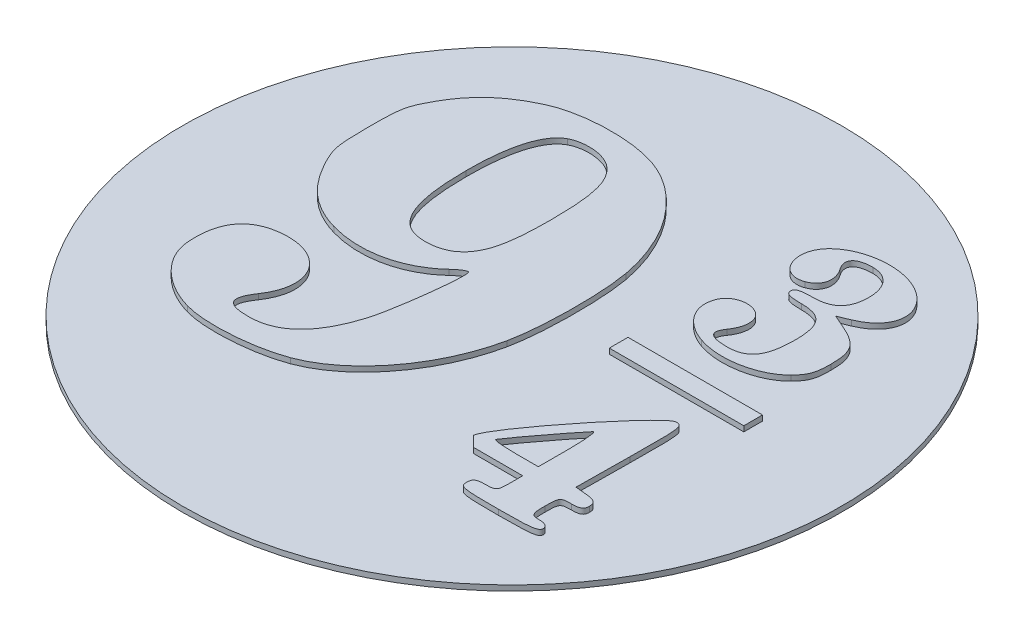
SolidWorks part; units mm, degrees
ref_plane "前视基准面" through (0, 0, 0) normal (0, 0, 1) x (1, 0, 0)
ref_plane "上视基准面" through (0, 0, 0) normal (0, 1, 0) x (1, 0, 0)
ref_plane "右视基准面" through (0, 0, 0) normal (1, 0, 0) x (0, 0, -1)
other "Configuration Table"
sketch "草图1" plane through (0, 0, 0) normal (0, 1, 0) x (1, 0, 0)
  circle A15 centre (0, 0) radius 24.7
  dimension "D1" = 49.4
extrude "凸台-拉伸3" add sketch "草图1" along normal blind 0.4
sketch "草图10" plane through (0, 0.4, 0) normal (0, 1, 0) x (1, 0, 0)
  line L0 (11.1751, -11.3536) -> (11.1751, -10.3736)
  line L1 (11.1751, -10.3736) -> (7.4816, -10.3736)
  line L2 (7.4816, -10.3736) -> (6.7076, -9.6036)
  line L3 (13.9572, -5.1236) -> (13.913, -9.1136)
  line L4 (13.913, -9.1136) -> (14.784, -9.2014)
  line L5 (9.4951, -9.2009) -> (11.1751, -9.2009)
  line L6 (11.1751, -9.2009) -> (11.1751, -6.9049)
  line L7 (6.1351, 1.8591) -> (6.1351, 2.5591)
  line L8 (6.1351, 2.5591) -> (11.1751, 2.5591)
  line L9 (11.1751, 2.5591) -> (16.2151, 2.5591)
  line L10 (16.2151, 2.5591) -> (16.2151, 1.8591)
  line L11 (16.2151, 1.8591) -> (16.2151, 1.1591)
  line L12 (16.2151, 1.1591) -> (11.1751, 1.1591)
  line L13 (11.1751, 1.1591) -> (6.1351, 1.1591)
  line L14 (6.1351, 1.1591) -> (6.1351, 1.8591)
  line L15 (13.3822, 12.0654) -> (12.5498, 11.7206)
  line L16 (12.5498, 11.7206) -> (13.6124, 11.2442)
  spline S0 degree 3 poles (9.4951, -12.8936) (9.4951, -12.4581) (9.6818, -12.3336) (10.3351, -12.3336) knots 0 0 0 0 1 1 1 1
  spline S1 degree 3 poles (10.3351, -12.3336) (11.1084, -12.3336) (11.1751, -12.2558) (11.1751, -11.3536) knots 0 0 0 0 1 1 1 1
  spline S2 degree 3 poles (6.7076, -9.6036) (6.7247, -8.5573) (12.6255, -1.1336) (13.4401, -1.1336) knots 0 0 0 0 1 1 1 1
  spline S3 degree 3 poles (13.4401, -1.1336) (13.9776, -1.1336) (13.9995, -1.3025) (13.9572, -5.1236) knots 0 0 0 0 1 1 1 1
  spline S4 degree 3 poles (14.784, -9.2014) (15.4287, -9.2663) (15.6551, -9.43) (15.6551, -9.8314) knots 0 0 0 0 1 1 1 1
  spline S5 degree 3 poles (15.6551, -9.8314) (15.6551, -10.2472) (15.4593, -10.3736) (14.8151, -10.3736) knots 0 0 0 0 1 1 1 1
  spline S6 degree 3 poles (14.8151, -10.3736) (14.0218, -10.3736) (13.9751, -10.4358) (13.9751, -11.4936) knots 0 0 0 0 1 1 1 1
  spline S7 degree 3 poles (13.9751, -11.4936) (13.9751, -12.5016) (14.0451, -12.6136) (14.6751, -12.6136) knots 0 0 0 0 1 1 1 1
  spline S8 degree 3 poles (14.6751, -12.6136) (15.1106, -12.6136) (15.3751, -12.7723) (15.3751, -13.0336) knots 0 0 0 0 1 1 1 1
  spline S9 degree 3 poles (15.3751, -13.0336) (15.3751, -13.3803) (14.8618, -13.4536) (12.4351, -13.4536) knots 0 0 0 0 1 1 1 1
  spline S10 degree 3 poles (12.4351, -13.4536) (9.6818, -13.4536) (9.4951, -13.4181) (9.4951, -12.8936) knots 0 0 0 0 1 1 1 1
  spline S11 degree 3 poles (11.1751, -6.9049) (11.1751, -5.6421) (11.0717, -4.7286) (10.9453, -4.8749) knots 0 0 0 0 1 1 1 1
  spline S12 degree 3 poles (10.9453, -4.8749) (10.1204, -5.8299) (7.8151, -8.8905) (7.8151, -9.0306) knots 0 0 0 0 1 1 1 1
  spline S13 degree 3 poles (7.8151, -9.0306) (7.8151, -9.1243) (8.5711, -9.2009) (9.4951, -9.2009) knots 0 0 0 0 1 1 1 1
  spline S14 degree 3 poles (-12.3952, -11.9089) (-14.6847, -11.26) (-16.3951, -9.5677) (-16.5468, -7.8009) knots 0 0 0 0 1 1 1 1
  spline S15 degree 3 poles (-16.5468, -7.8009) (-16.7597, -5.3213) (-15.7908, -3.9165) (-13.7055, -3.6815) knots 0 0 0 0 1 1 1 1
  spline S16 degree 3 poles (-13.7055, -3.6815) (-10.5072, -3.321) (-8.8054, -5.8906) (-10.5459, -8.452) knots 0 0 0 0 1 1 1 1
  spline S17 degree 3 poles (-10.5459, -8.452) (-11.4486, -9.7804) (-11.1284, -10.3214) (-9.4406, -10.3199) knots 0 0 0 0 1 1 1 1
  spline S18 degree 3 poles (-9.4406, -10.3199) (-7.2943, -10.3179) (-5.8007, -8.8893) (-4.9047, -5.9809) knots 0 0 0 0 1 1 1 1
  spline S19 degree 3 poles (-4.9047, -5.9809) (-4.435, -4.4565) (-3.8216, 0.5691) (-4.0743, 0.8218) knots 0 0 0 0 1 1 1 1
  spline S20 degree 3 poles (-4.0743, 0.8218) (-4.1604, 0.9078) (-4.5759, 0.6553) (-4.9978, 0.2606) knots 0 0 0 0 1 1 1 1
  spline S21 degree 3 poles (-4.9978, 0.2606) (-6.8052, -1.4303) (-9.5234, -2.0146) (-12.0892, -1.2637) knots 0 0 0 0 1 1 1 1
  spline S22 degree 3 poles (-12.0892, -1.2637) (-14.0128, -0.7008) (-15.3618, 0.4177) (-16.411, 2.3195) knots 0 0 0 0 1 1 1 1
  spline S23 degree 3 poles (-16.411, 2.3195) (-17.1629, 3.6826) (-17.2385, 4.061) (-17.2415, 6.4791) knots 0 0 0 0 1 1 1 1
  spline S24 degree 3 poles (-17.2415, 6.4791) (-17.2446, 8.9035) (-17.1719, 9.2709) (-16.4199, 10.6283) knots 0 0 0 0 1 1 1 1
  spline S25 degree 3 poles (-16.4199, 10.6283) (-15.41, 12.4515) (-14.1192, 13.6185) (-12.0777, 14.5541) knots 0 0 0 0 1 1 1 1
  spline S26 degree 3 poles (-12.0777, 14.5541) (-10.0857, 15.4669) (-6.5529, 15.5739) (-4.3032, 14.7893) knots 0 0 0 0 1 1 1 1
  spline S27 degree 3 poles (-4.3032, 14.7893) (-1.2608, 13.7283) (1.2079, 10.4902) (1.9116, 6.6376) knots 0 0 0 0 1 1 1 1
  spline S28 degree 3 poles (1.9116, 6.6376) (2.3293, 4.3506) (2.2838, -0.011) (1.8193, -2.2019) knots 0 0 0 0 1 1 1 1
  spline S29 degree 3 poles (1.8193, -2.2019) (0.9187, -6.4498) (-1.9261, -10.1925) (-5.1777, -11.4075) knots 0 0 0 0 1 1 1 1
  spline S30 degree 3 poles (-5.1777, -11.4075) (-7.2474, -12.1809) (-10.6108, -12.4145) (-12.3952, -11.9089) knots 0 0 0 0 1 1 1 1
  spline S31 degree 3 poles (-5.8229, 1.7234) (-4.7498, 2.5676) (-4.3741, 4.0186) (-4.3741, 7.3191) knots 0 0 0 0 1 1 1 1
  spline S32 degree 3 poles (-4.3741, 7.3191) (-4.3741, 10.6195) (-4.7498, 12.0705) (-5.8229, 12.9147) knots 0 0 0 0 1 1 1 1
  spline S33 degree 3 poles (-5.8229, 12.9147) (-6.6088, 13.5328) (-8.1303, 13.6564) (-9.0297, 13.1751) knots 0 0 0 0 1 1 1 1
  spline S34 degree 3 poles (-9.0297, 13.1751) (-10.1622, 12.569) (-10.7607, 10.5331) (-10.7514, 7.3191) knots 0 0 0 0 1 1 1 1
  spline S35 degree 3 poles (-10.7514, 7.3191) (-10.7421, 4.1138) (-10.2508, 2.3291) (-9.1692, 1.5715) knots 0 0 0 0 1 1 1 1
  spline S36 degree 3 poles (-9.1692, 1.5715) (-8.3242, 0.9797) (-6.6732, 1.0547) (-5.8229, 1.7234) knots 0 0 0 0 1 1 1 1
  spline S37 degree 3 poles (9.0751, 5.1377) (7.3764, 5.7331) (6.4995, 7.0481) (6.9721, 8.2912) knots 0 0 0 0 1 1 1 1
  spline S38 degree 3 poles (6.9721, 8.2912) (7.2817, 9.1056) (8.36, 9.4567) (9.189, 9.013) knots 0 0 0 0 1 1 1 1
  spline S39 degree 3 poles (9.189, 9.013) (9.8923, 8.6366) (9.9473, 7.6895) (9.3179, 6.7909) knots 0 0 0 0 1 1 1 1
  spline S40 degree 3 poles (9.3179, 6.7909) (8.7686, 6.0067) (9.132, 5.6476) (10.4751, 5.6476) knots 0 0 0 0 1 1 1 1
  spline S41 degree 3 poles (10.4751, 5.6476) (11.9632, 5.6476) (12.5751, 6.519) (12.5751, 8.6383) knots 0 0 0 0 1 1 1 1
  spline S42 degree 3 poles (12.5751, 8.6383) (12.5751, 10.5626) (12.0247, 11.2391) (10.4592, 11.2391) knots 0 0 0 0 1 1 1 1
  spline S43 degree 3 poles (10.4592, 11.2391) (9.54, 11.2391) (9.2151, 11.3487) (9.2151, 11.6591) knots 0 0 0 0 1 1 1 1
  spline S44 degree 3 poles (9.2151, 11.6591) (9.2151, 11.9694) (9.54, 12.0791) (10.4592, 12.0791) knots 0 0 0 0 1 1 1 1
  spline S45 degree 3 poles (10.4592, 12.0791) (11.8959, 12.0791) (12.5751, 12.7531) (12.5751, 14.1791) knots 0 0 0 0 1 1 1 1
  spline S46 degree 3 poles (12.5751, 14.1791) (12.5751, 15.4663) (11.8778, 16.2791) (10.7735, 16.2791) knots 0 0 0 0 1 1 1 1
  spline S47 degree 3 poles (10.7735, 16.2791) (9.535, 16.2791) (9.0919, 15.7395) (9.662, 14.9256) knots 0 0 0 0 1 1 1 1
  spline S48 degree 3 poles (9.662, 14.9256) (10.2807, 14.0423) (10.06, 13.1211) (9.1536, 12.8036) knots 0 0 0 0 1 1 1 1
  spline S49 degree 3 poles (9.1536, 12.8036) (7.4984, 12.2239) (6.5755, 14.5049) (7.9209, 15.8503) knots 0 0 0 0 1 1 1 1
  spline S50 degree 3 poles (7.9209, 15.8503) (9.452, 17.3814) (12.7011, 17.4691) (14.3195, 16.0231) knots 0 0 0 0 1 1 1 1
  spline S51 degree 3 poles (14.3195, 16.0231) (15.803, 14.6976) (15.3751, 12.8909) (13.3822, 12.0654) knots 0 0 0 0 1 1 1 1
  spline S52 degree 3 poles (13.6124, 11.2442) (15.1071, 10.5741) (15.4828, 10.0063) (15.4828, 8.417) knots 0 0 0 0 1 1 1 1
  spline S53 degree 3 poles (15.4828, 8.417) (15.4828, 7.294) (15.3397, 6.8928) (14.7019, 6.227) knots 0 0 0 0 1 1 1 1
  spline S54 degree 3 poles (14.7019, 6.227) (13.5039, 4.9766) (10.9469, 4.4816) (9.0751, 5.1377) knots 0 0 0 0 1 1 1 1
extrude "凸台-拉伸-9-4-3" add sketch "草图10" along normal blind 0.4
